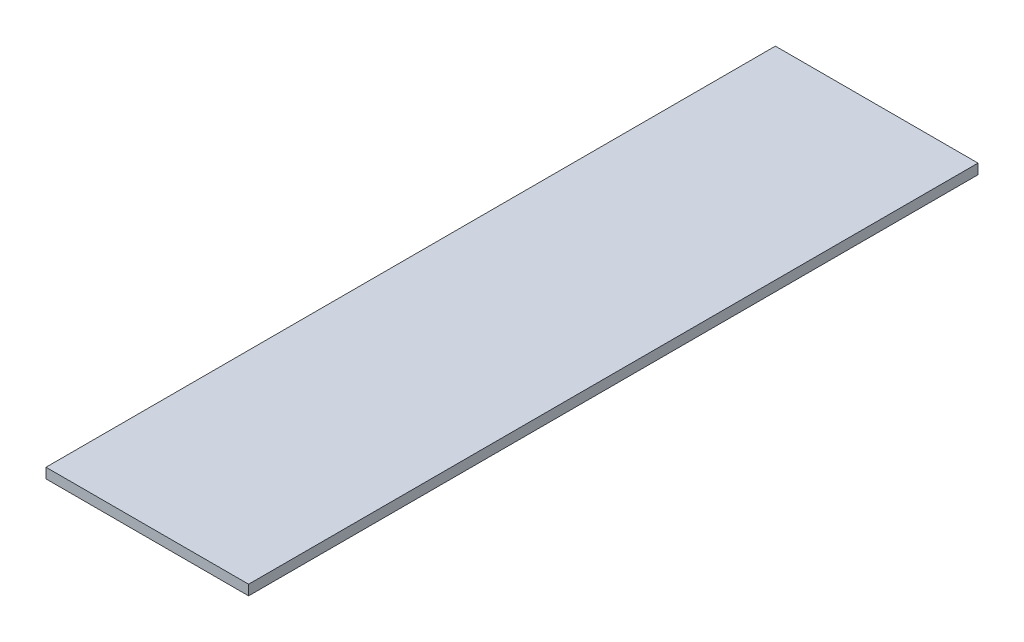
SolidWorks part; units mm, degrees
ref_plane "Front Plane" through (0, 0, 0) normal (0, 0, 1) x (1, 0, 0)
ref_plane "Top Plane" through (0, 0, 0) normal (0, 1, 0) x (1, 0, 0)
ref_plane "Right Plane" through (0, 0, 0) normal (1, 0, 0) x (0, 0, -1)
sketch "Sketch1" plane through (0, 0, 0) normal (0, 1, 0) x (1, 0, 0)
  line L1 (0, 0) -> (127, 0)
  line L2 (0, 0) -> (0, 457.2)
  line L3 (0, 457.2) -> (127, 457.2)
  line L4 (127, 0) -> (127, 457.2)
  dimension "D1" = 127
  dimension "D2" = 457.2
extrude "Boss-Extrude1" add sketch "Sketch1" along normal blind 6.35
